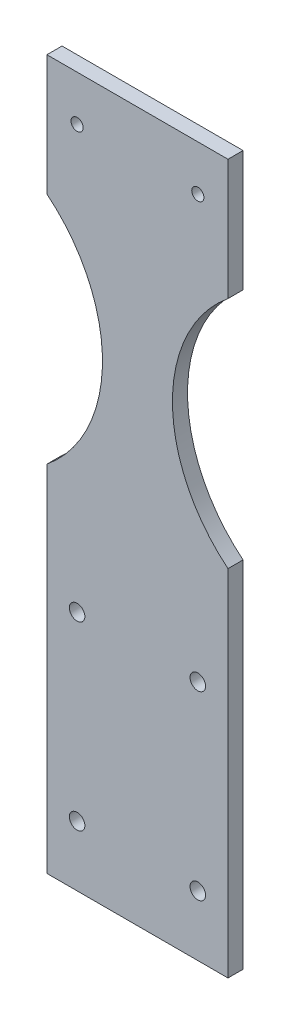
SolidWorks part; units mm, degrees
ref_plane "Front Plane" through (0, 0, 0) normal (0, 0, 1) x (1, 0, 0)
ref_plane "Top Plane" through (0, 0, 0) normal (0, 1, 0) x (1, 0, 0)
ref_plane "Right Plane" through (0, 0, 0) normal (1, 0, 0) x (0, 0, -1)
sketch "Sketch1" plane through (0, 0, 0) normal (0, 0, 1) x (1, 0, 0)
  line L1 (-38.1, -149.225) -> (38.1, -149.225)
  line L2 (-38.1, -149.225) -> (-38.1, 149.225)
  line L3 (-38.1, 149.225) -> (38.1, 149.225)
  line L4 (38.1, -149.225) -> (38.1, 149.225)
  line L5 (-38.1, -149.225) -> (38.1, 149.225) construction
  line L6 (-38.1, 149.225) -> (38.1, -149.225) construction
  point P0 (0, 0)
  dimension "D1" = 298.45
  dimension "D2" = 76.2
extrude "Boss-Extrude1" add sketch "Sketch1" along normal blind 6.35
sketch "Sketch2" plane through (0, 0, 0) normal (0, 0, -1) x (-1, 0, 0)
  line L0 (0, 149.225) -> (0, -149.225) construction
  line L1 (-38.1, 149.225) -> (38.1, 149.225) construction
  line L2 (38.1, -149.225) -> (-38.1, -149.225) construction
  line L3 (-25.4, -123.825) -> (-25.4, -47.625)
  line L4 (-38.1, -149.225) -> (-38.1, 149.225) construction
  line L5 (25.4, -123.825) -> (25.4, -47.625)
  line L6 (-25.4, 130.175) -> (25.4, 130.175)
  point P16 (0, 130.175)
  dimension "D1" = 76.2
  dimension "D2" = 12.7
  dimension "D3" = 25.4
  dimension "D4" = 12.7
  dimension "D5" = 19.05
hole_wizard "1/4-20 Tapped Hole1" positions "Sketch4" profile "Sketch5" tap size "1/4-20" standard "ANSI Inch" end condition up to next
sketch "Sketch4" plane through (0, 0, 0) normal (0, 0, -1) x (-1, 0, 0)
  point P0 (-25.4, 130.175)
  point P3 (25.4, 130.175)
  point P6 (25.4, -47.625)
  point P9 (25.4, -123.825)
  point P12 (-25.4, -123.825)
  point P15 (-25.4, -47.625)
sketch "Sketch5" plane through (25.4, 130.175, 0) normal (1, 0, 0) x (0, 1, 0)
  line L0 (0, 0) -> (0, 6.35)
  line L1 (0, 6.35) -> (2.5527, 6.35)
  line L2 (2.5527, 6.35) -> (2.5527, 0)
  line L5 (2.5527, 0) -> (0, 0)
  line L11 (0, -6.35) -> (0, 107.95) construction
  dimension "Thru Tap Drill Dia." = 5.1054
  dimension "Thru Tap Drill Depth" = 6.35
cosmetic thread "Hole Thread1" parameters "D2"=6.35
cosmetic thread "Hole Thread2" parameters "D2"=6.35
cosmetic thread "Hole Thread3" parameters "D2"=6.35
cosmetic thread "Hole Thread4" parameters "D2"=6.35
cosmetic thread "Hole Thread5" parameters "D2"=6.35
cosmetic thread "Hole Thread6" parameters "D2"=6.35
sketch "Sketch6" plane through (0, 0, 0) normal (0, 0, -1) x (-1, 0, 0)
  line L0 (-38.1, -149.225) -> (-38.1, 149.225) construction
  line L2 (-38.1, 149.225) -> (38.1, 149.225) construction
  line L3 (0, 149.225) -> (0, -149.225) construction
  line L4 (-38.1, 98.425) -> (-38.1, 0)
  line L5 (38.1, 98.425) -> (38.1, 0)
  arc A0 (-38.1, 98.425) -> (-38.1, 0) centre (-78.2295, 49.2125) cw
  arc A1 (38.1, 98.425) -> (38.1, 0) centre (78.2295, 49.2125) ccw
  dimension "D1" = 50.8
  dimension "D2" = 63.5
extrude "Cut-Extrude1" cut sketch "Sketch6" against normal through all
hole_wizard "F (0.257) Diameter Hole1" positions "Sketch8" profile "Sketch9" hole size "F" standard "ANSI Inch" end condition through all
sketch "Sketch8" plane through (0, 0, 0) normal (0, 0, -1) x (-1, 0, 0)
  point P0 (-25.4, -47.625)
  point P3 (25.4, -47.625)
  point P6 (25.4, -123.825)
  point P9 (-25.4, -123.825)
sketch "Sketch9" plane through (25.4, -47.625, 0) normal (1, 0, 0) x (0, 1, 0)
  line L0 (0, 0) -> (0, 6.35)
  line L1 (0, 6.35) -> (3.2639, 6.35)
  line L2 (3.2639, 6.35) -> (3.2639, 0)
  line L5 (3.2639, 0) -> (0, 0)
  line L11 (0, -6.35) -> (0, 107.95) construction
  dimension "Thru Hole Dia." = 6.5278
  dimension "Thru Hole Depth" = 6.35
